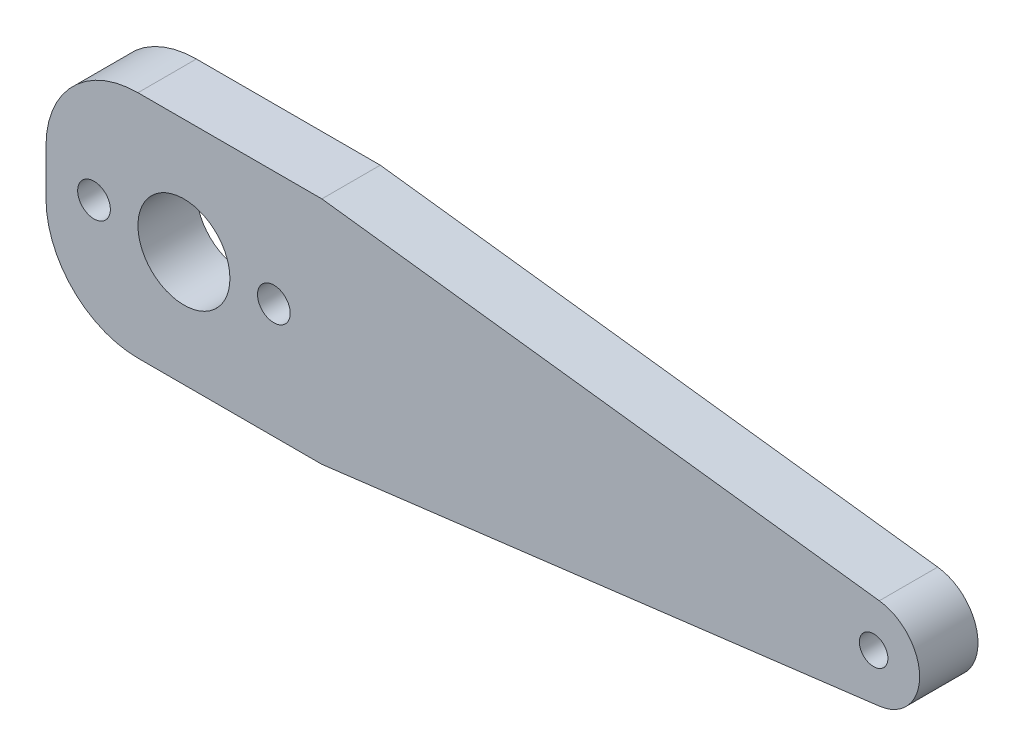
SolidWorks part; units mm, degrees
ref_plane "Front Plane" through (0, 0, 0) normal (0, 0, 1) x (1, 0, 0)
ref_plane "Top Plane" through (0, 0, 0) normal (0, 1, 0) x (1, 0, 0)
ref_plane "Right Plane" through (0, 0, 0) normal (1, 0, 0) x (0, 0, -1)
sketch "Sketch1" plane through (0, 0, 0) normal (0, 0, 1) x (1, 0, 0)
  line L0 (30, 25) -> (90.617, 17.4617)
  line L1 (0, 0) -> (30, 0)
  line L2 (0, 0) -> (0, 25)
  line L3 (0, 25) -> (30, 25)
  line L5 (30, 0) -> (90.617, 7.5382)
  circle A0 centre (15, 12.4999) radius 9.779
  circle A1 centre (90, 12.4999) radius 1.55
  circle A2 centre (5.221, 12.4999) radius 1.778
  circle A3 centre (24.779, 12.4999) radius 1.778
  circle A4 centre (90, 12.4999) radius 5
  circle A5 centre (15, 12.4999) radius 5
  dimension "D3" = 19.558
  dimension "D4" = 3.556
  dimension "D5" = 3.556
  dimension "D7" = 10
  dimension "D2" = 3.1
  dimension "D9" = 10
  dimension "D1" = 25
  dimension "D6" = 75
  dimension "D8" = 15
extrude "Boss-Extrude1" add sketch "Sketch1" along normal blind 6.35
fillet "Fillet1" radius 10 2 edges at (0, 0, 3.175) (0, 25, 3.175)
